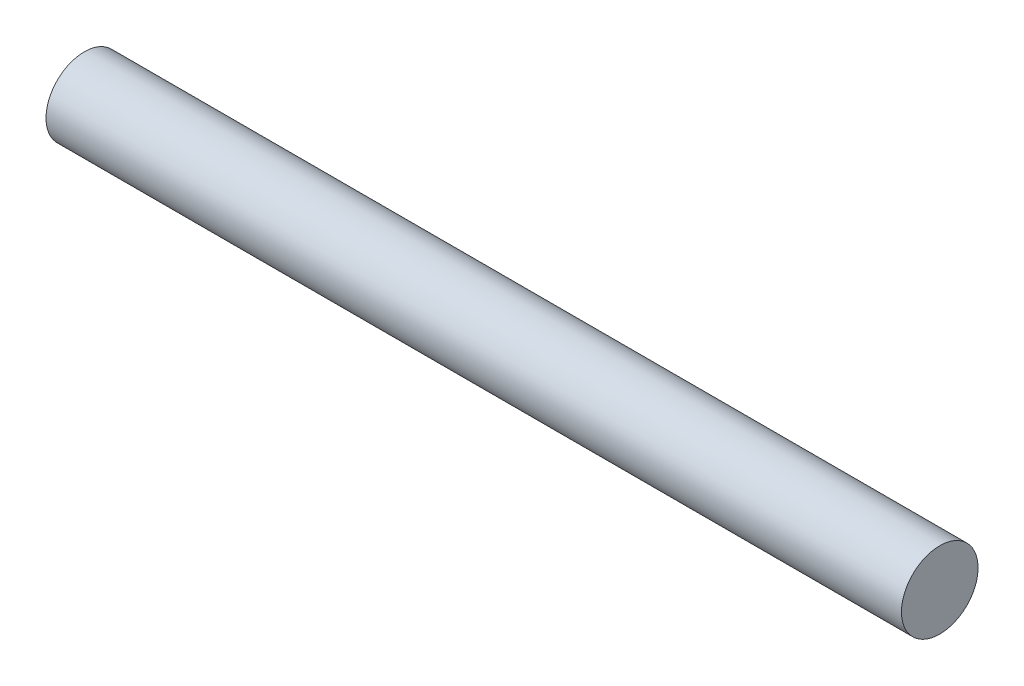
SolidWorks part; units mm, degrees
ref_plane "正面" through (0, 0, 0) normal (0, 0, 1) x (1, 0, 0)
ref_plane "平面" through (0, 0, 0) normal (0, 1, 0) x (1, 0, 0)
ref_plane "右側面" through (0, 0, 0) normal (1, 0, 0) x (0, 0, -1)
sketch "ｽｹｯﾁ1" plane through (0, 0, 0) normal (0, 0, 1) x (1, 0, 0)
  line L0 (0, 0) -> (33.5, 0) construction
  line L1 (0, 0) -> (0, 3)
  line L2 (0, 3) -> (29.5, 3)
  line L3 (29.5, 3) -> (29.5, 2) construction
  line L4 (29.5, 2) -> (30.5, 2) construction
  line L5 (30.5, 2) -> (30.5, 3) construction
  line L6 (30.5, 3) -> (33.5, 3)
  line L7 (33.5, 3) -> (33.5, 0)
  line L8 (0, 0) -> (33.5, 0)
  line L9 (29.5, 3) -> (30.5, 3)
  dimension "D1" = 1
  dimension "D2" = 3
  dimension "D3" = 3
  dimension "D4" = 29.5
revolve "回転1" add sketch "ｽｹｯﾁ1" angle 360 about L0
mirror "ﾐﾗｰ1" about plane through (0, 0, 0) normal (1, 0, 0) of bodies 105
